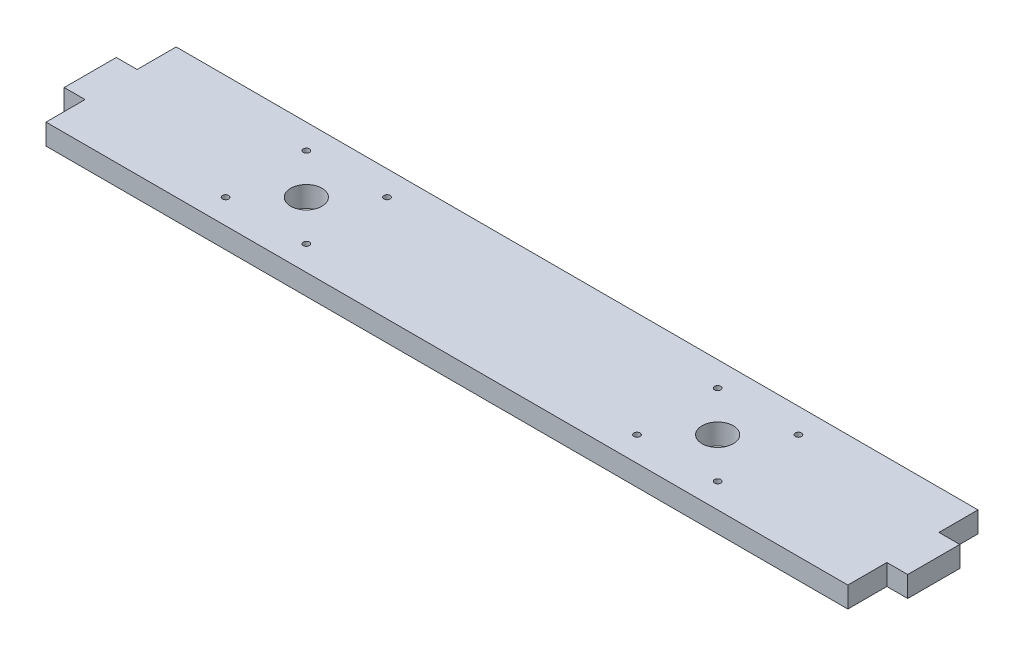
SolidWorks part; units mm, degrees
material "Acrylic (Medium-high impact)"
ref_plane "Front Plane" through (0, 0, 0) normal (0, 0, 1) x (1, 0, 0)
ref_plane "Top Plane" through (0, 0, 0) normal (0, 1, 0) x (1, 0, 0)
ref_plane "Right Plane" through (0, 0, 0) normal (1, 0, 0) x (0, 0, -1)
sketch "Sketch1" plane through (0, 0, 0) normal (0, 1, 0) x (1, 0, 0)
  line L0 (154, 0) -> (154, 50) construction
  line L1 (0, 0) -> (308, 0)
  line L2 (0, 0) -> (0, 50)
  line L3 (0, 50) -> (308, 50)
  line L4 (308, 0) -> (308, 50)
  line L5 (0, 25) -> (308, 25) construction
  circle A0 centre (75, 25) radius 6
  circle A1 centre (59.5, 40.5) radius 1.2
  circle A2 centre (90.5, 40.5) radius 1.2
  circle A3 centre (59.5, 9.5) radius 1.2
  circle A4 centre (90.5, 9.5) radius 1.2
  circle A5 centre (217.5, 9.5) radius 1.2
  circle A6 centre (248.5, 9.5) radius 1.2
  circle A7 centre (217.5, 40.5) radius 1.2
  circle A8 centre (233, 25) radius 6
  circle A9 centre (248.5, 40.5) radius 1.2
  dimension "D3" = 12
  dimension "D9" = 2.4
  dimension "D1" = 308
  dimension "D2" = 50
  dimension "D4" = 2
  dimension "D5" = 15.5
  dimension "D6" = 15.5
  dimension "D7" = 2
  dimension "D8" = 2
extrude "Boss-Extrude1" add sketch "Sketch1" along normal blind 8
sketch "Sketch2" plane through (0, 8, 0) normal (0, 1, 0) x (-1, 0, 0)
  line L0 (0, -50) -> (0, 0) construction
  line L1 (0, -35) -> (8, -35)
  line L2 (0, -35) -> (0, -15)
  line L3 (0, -15) -> (8, -15)
  line L4 (8, -35) -> (8, -15)
  line L5 (-154, -50) -> (-154, 0) construction
  line L6 (-308, -50) -> (0, -50) construction
  line L7 (0, 0) -> (-308, 0) construction
  line L8 (-316, -35) -> (-316, -15)
  line L9 (-308, -15) -> (-316, -15)
  line L10 (-308, -35) -> (-308, -15)
  line L11 (-308, -35) -> (-316, -35)
  point P6 (8, -25)
  point P7 (0, -25)
  point P18 (-308, -25)
  point P19 (-316, -25)
  dimension "D1" = 20
  dimension "D2" = 8
extrude "Boss-Extrude2" add sketch "Sketch2" against normal blind 8
